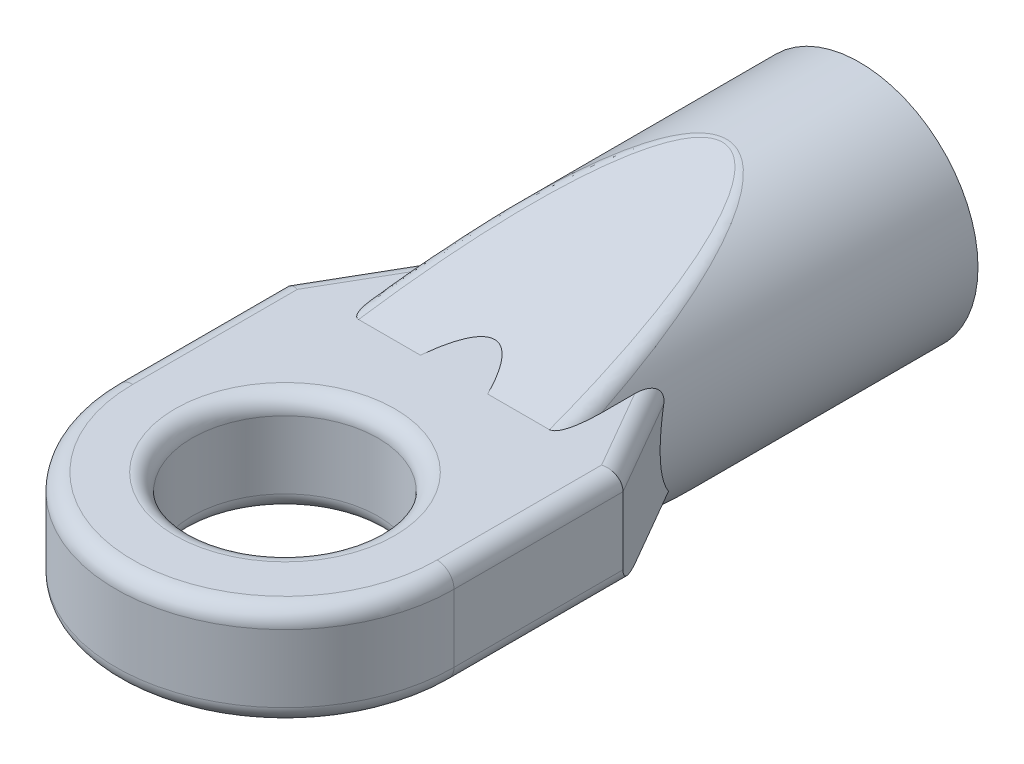
SolidWorks part; units mm, degrees
ref_plane "Front" through (0, 0, 0) normal (0, 0, 1) x (1, 0, 0)
ref_plane "Top" through (0, 0, 0) normal (0, 1, 0) x (1, 0, 0)
ref_plane "Right" through (0, 0, 0) normal (1, 0, 0) x (0, 0, -1)
sketch "Sketch1" plane through (0, 0, 0) normal (0, 0, 1) x (1, 0, 0)
  circle A0 centre (0, 0) radius 3.5
  circle A1 centre (0, 0) radius 1.8
  dimension "D1" = 7
  dimension "D2" = 3.6
extrude "Boss-Extrude1" add sketch "Sketch1" along normal blind 12
sketch "Sketch2" plane through (0, 0, 0) normal (0, 1, 0) x (1, 0, 0)
  line L0 (-3.5, -12) -> (3.5, -12) construction
  line L2 (-5, -17) -> (-5, -12)
  line L3 (-5, -12) -> (5, -12)
  line L4 (5, -17) -> (5, -12)
  arc A0 (-5, -17) -> (5, -17) centre (0, -17) ccw
  dimension "D1" = 10
  dimension "D2" = 5
extrude "Boss-Extrude2" add sketch "Sketch2" along normal mid plane 3
sketch "Sketch3" plane through (0, 0, 0) normal (0, 1, 0) x (1, 0, 0)
  line L0 (5, -12) -> (0, -3.3397)
  line L1 (0, -3.3397) -> (-5, -12)
  line L2 (-5, -12) -> (5, -12)
  dimension "D1" = 60
extrude "Boss-Extrude3" add sketch "Sketch3" along normal mid plane 3
sketch "Sketch5" plane through (0, 0, 0) normal (1, 0, 0) x (0, 0, -1)
  line L0 (-12, 1.5) -> (-4, 3.5)
  line L1 (0, 3.5) -> (-12, 3.5) construction
  line L2 (-4, 3.5) -> (-12, 3.5)
  line L3 (-12, 3.5) -> (-12, 1.5)
  dimension "D1" = 8
extrude "Cut-Extrude1" cut sketch "Sketch5" against normal mid plane 10
mirror "Mirror1" about plane through (0, 0, 0) normal (0, 1, 0) of "Cut-Extrude1"
sketch "Sketch6" plane through (0, 1.5, 0) normal (0, 1, 0) x (1, 0, 0)
  circle A0 centre (0, -17) radius 2.75
  arc A1 (-5, -17) -> (5, -17) centre (0, -17) ccw construction
  dimension "D1" = 5.5
extrude "Cut-Extrude2" cut sketch "Sketch6" against normal through all
fillet "Fillet1" radius 0.5 13 edges at (-5, -1.5, 14.5) (0, -1.5, 22) (-5, 1.5, 14.5) (5, 1.5, 14.5) (0, 3.5, 4) (0, -3.5, 4) (-4.0811, 1.5, 10.4085) (-4.0811, -1.5, 10.4085) (5, -1.5, 14.5) (0, -1.5, 19.75) (0, 1.5, 19.75) (4.0811, 1.5, 10.4085) (0, 1.5, 22)
